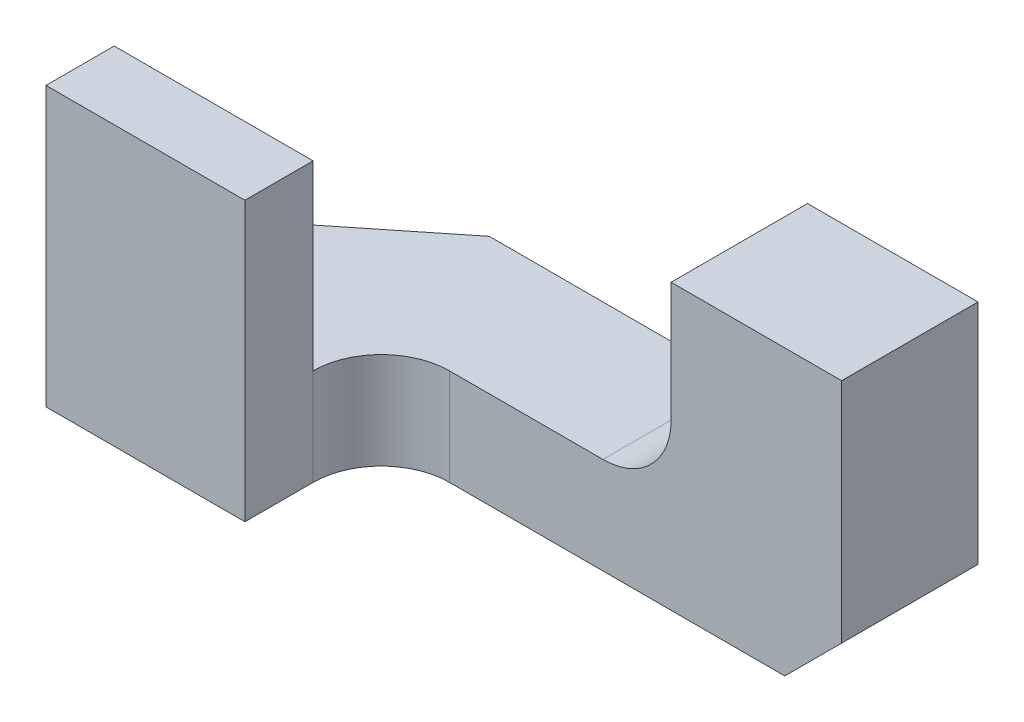
SolidWorks part; units mm, degrees
ref_plane "Front Plane" through (0, 0, 0) normal (0, 0, 1) x (1, 0, 0)
ref_plane "Top Plane" through (0, 0, 0) normal (0, 1, 0) x (1, 0, 0)
ref_plane "Right Plane" through (0, 0, 0) normal (1, 0, 0) x (0, 0, -1)
sketch "Sketch1" plane through (0, 0, 0) normal (0, 1, 0) x (1, 0, 0)
  line L1 (7.366, -3.048) -> (-7.366, -3.048)
  line L2 (7.366, -3.048) -> (7.366, 3.048)
  line L3 (7.366, 3.048) -> (-7.366, 3.048)
  line L4 (-7.366, -3.048) -> (-7.366, 3.048)
  line L5 (7.366, -3.048) -> (-7.366, 3.048) construction
  line L6 (7.366, 3.048) -> (-7.366, -3.048) construction
  point P0 (0, 0)
  dimension "D1" = 14.732
  dimension "D2" = 6.096
extrude "Boss-Extrude1" add sketch "Sketch1" along normal blind 6.35
sketch "Sketch4" plane through (0, 6.35, 0) normal (0, 1, 0) x (1, 0, 0)
  line L0 (-2.921, 0) -> (-1.397, 0)
  line L1 (7.366, -3.048) -> (-2.921, -3.048)
  line L2 (7.366, -3.048) -> (7.366, 0)
  line L3 (7.366, 0) -> (-2.921, 0)
  line L4 (-2.921, -3.048) -> (-2.921, 0)
  line L5 (-1.397, 0) -> (-1.397, -3.048)
  line L6 (-2.921, -1.524) -> (-2.921, 0)
  circle A0 centre (-1.397, -1.524) radius 1.524
  line M2 (-7.366, -3.048) -> (7.366, -3.048)
  line M3 (7.366, -3.048) -> (7.366, 3.048)
  dimension "D1" = 3.048
  dimension "D2" = 10.287
  dimension "D3" = 1.524
extrude "Cut-Extrude2" cut sketch "Sketch4" against normal through all contours A0 L1 L3 M3 | L5 A0 | L5 A0 | A0 L4 M2
sketch "Sketch3" plane through (0, 6.35, 0) normal (0, 1, 0) x (1, 0, 0)
  line L0 (-7.366, -3.048) -> (-2.921, -3.048) construction
  line L1 (-7.366, 3.048) -> (3.556, 3.048)
  line L2 (-7.366, 3.048) -> (-7.366, -3.048)
  line L3 (-7.366, -3.048) -> (3.556, -3.048)
  line L4 (3.556, 3.048) -> (3.556, -3.048)
  dimension "D1" = 10.922
extrude "Cut-Extrude1" cut sketch "Sketch3" against normal blind 2.667
sketch "Sketch8" plane through (0, 3.683, 0) normal (0, 1, 0) x (1, 0, 0)
  line L1 (-7.366, 3.048) -> (-7.366, -3.048) construction
  line L3 (3.556, 3.048) -> (-7.366, 3.048) construction
  line L4 (-3.556, 3.048) -> (-7.366, 0)
  line L5 (-7.366, 3.048) -> (-3.556, 3.048)
  line M4 (3.556, 3.048) -> (-7.366, 3.048)
  line M5 (-7.366, 3.048) -> (-7.366, -3.048)
  dimension "D1" = 3.81
extrude "Cut-Extrude3" cut sketch "Sketch8" against normal through all contours L4 M4 M5
sketch "Sketch9" plane through (0, 3.683, 0) normal (0, 1, 0) x (1, 0, 0)
  line L0 (-7.366, 0) -> (-7.366, -3.048) construction
  line L1 (-2.921, -3.048) -> (-7.366, -3.048)
  line L2 (-2.921, -3.048) -> (-2.921, -1.524)
  line L3 (-2.921, -1.524) -> (-7.366, -1.524)
  line L4 (-7.366, -3.048) -> (-7.366, -1.524)
  dimension "D1" = 1.524
extrude "Boss-Extrude2" add sketch "Sketch9" along normal blind 2.54
sketch "Sketch10" plane through (0, 0, -3.048) normal (0, 0, -1) x (-1, 0, 0)
  line L0 (-7.366, 1.27) -> (-6.096, 0)
  line L1 (-7.366, 6.35) -> (-7.366, 0) construction
  line L2 (-7.366, 0) -> (3.556, 0) construction
  line L3 (-6.096, 0) -> (-7.366, 0)
  line L4 (-7.366, 0) -> (-7.366, 1.27)
  dimension "D1" = 1.27
  dimension "D2" = 1.27
extrude "Cut-Extrude4" cut sketch "Sketch10" against normal through all
sketch "Sketch12" plane through (0, 0, -3.048) normal (0, 0, -1) x (-1, 0, 0)
  line L0 (-2.032, 2.159) -> (-2.032, 3.683)
  line L2 (3.556, 3.683) -> (-3.556, 3.683)
  line L3 (3.556, 3.683) -> (3.556, 2.159)
  line L4 (3.556, 2.159) -> (-3.556, 2.159)
  line L5 (-3.556, 3.683) -> (-3.556, 2.159)
  line L6 (-2.032, 2.159) -> (-3.556, 2.159)
  line L7 (3.556, 3.683) -> (2.921, 3.683)
  line L8 (3.556, 3.683) -> (2.921, 3.683)
  line L9 (3.556, 3.683) -> (3.556, 2.159)
  line L10 (3.556, 2.159) -> (2.921, 2.159)
  line L11 (2.921, 3.683) -> (2.921, 2.159)
  circle A0 centre (-2.032, 3.683) radius 1.524
  line M4 (3.556, 0) -> (3.556, 3.683)
  line M5 (3.556, 3.683) -> (-3.556, 3.683)
  dimension "D1" = 1.524
  dimension "D2" = 1.524
  dimension "D3" = 0.635
extrude "Cut-Extrude5" cut sketch "Sketch12" against normal blind 4.191 contours A0 L4 M4 M5 | L0 A0 L2 | A0 L0 M5
sketch "Sketch13" plane through (0, 0, -3.048) normal (0, 0, -1) x (-1, 0, 0)
  line L1 (2.921, 2.159) -> (7.366, 2.159)
  line L2 (2.921, 2.159) -> (2.921, 3.683)
  line L3 (2.921, 3.683) -> (7.366, 3.683)
  line L4 (7.366, 2.159) -> (7.366, 3.683)
  dimension "D1" = 4.445
sketch "Sketch14" plane through (0, 0, 1.143) normal (0, 0, -1) x (-1, 0, 0)
  line L0 (2.8726, 3.683) -> (2.921, 3.683)
sketch "Sketch15" plane through (0, 0, 1.143) normal (0, 0, -1) x (-1, 0, 0)
  line L1 (2.921, 2.159) -> (2.8726, 2.159)
  line L2 (2.921, 2.159) -> (2.921, 3.683)
  line L3 (2.921, 3.683) -> (2.8726, 3.683)
  line L4 (2.8726, 2.159) -> (2.8726, 3.683)
extrude "Cut-Extrude10" cut sketch "Sketch15" against normal through all
extrude "Cut-Extrude11" cut sketch "Sketch13" against normal blind 4.572
